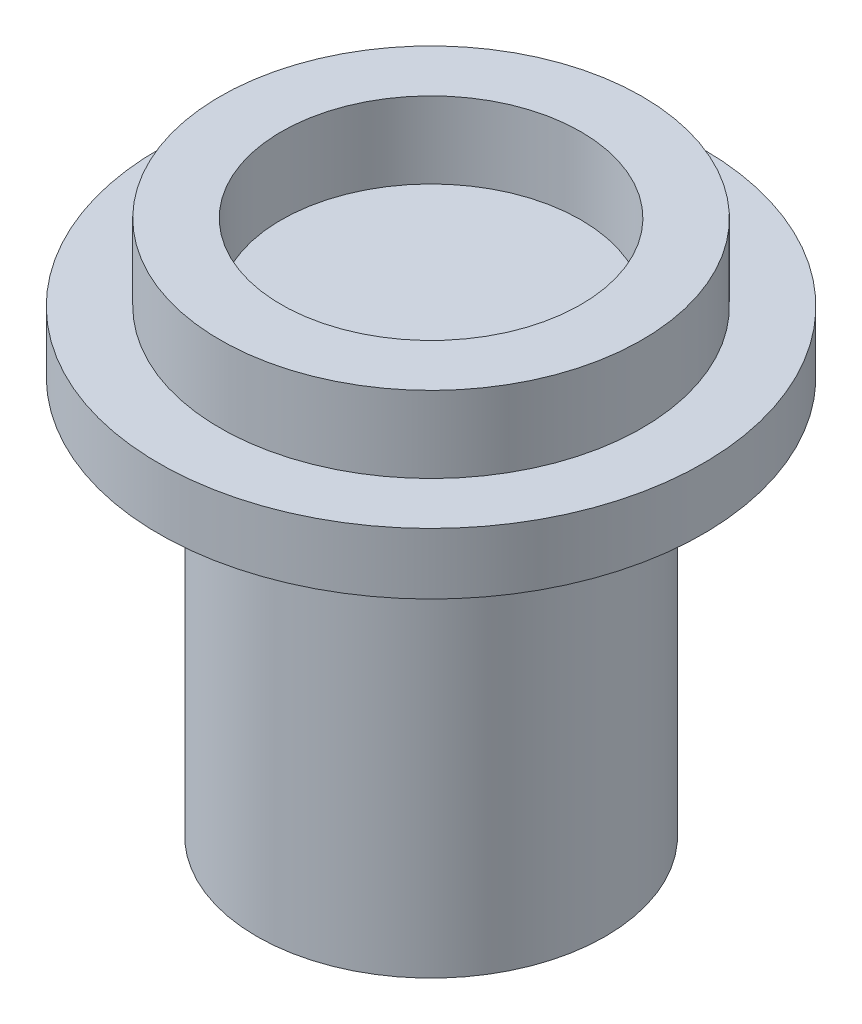
SolidWorks part; units mm, degrees
ref_plane "Front Plane" through (0, 0, 0) normal (0, 0, 1) x (1, 0, 0)
ref_plane "Top Plane" through (0, 0, 0) normal (0, 1, 0) x (1, 0, 0)
ref_plane "Right Plane" through (0, 0, 0) normal (1, 0, 0) x (0, 0, -1)
sketch "Sketch2" plane through (0, 0, 0) normal (0, 0, 1) x (1, 0, 0)
  line L0 (0, -1.7884) -> (0, 9.1065) construction
  line L1 (1.55, 1.1803) -> (1.55, 7.6803)
  line L2 (1.55, 7.6803) -> (0, 7.6803)
  line L3 (1.55, 1.1803) -> (2.85, 1.1803)
  line L4 (2.85, 1.1803) -> (2.85, 7.6803)
  line L5 (2.85, 7.6803) -> (4.45, 7.6803)
  line L6 (4.45, 7.6803) -> (4.45, 8.6803)
  line L7 (4.45, 8.6803) -> (3.45, 8.6803)
  line L8 (3.45, 8.6803) -> (3.45, 9.9283)
  line L9 (3.45, 9.9283) -> (2.45, 9.9283)
  line L10 (2.45, 9.9283) -> (2.45, 8.6803)
  line L11 (2.45, 8.6803) -> (0, 8.6803)
  line L12 (0, 7.6803) -> (0, 8.6803)
  dimension "D1" = 6.5
  dimension "D2" = 1.55
  dimension "D3" = 1.3
  dimension "D4" = 1.6
  dimension "D5" = 1
  dimension "D6" = 1
  dimension "D7" = 1
  dimension "D8" = 1
revolve "Revolve3" add sketch "Sketch2" angle 360 about L0
